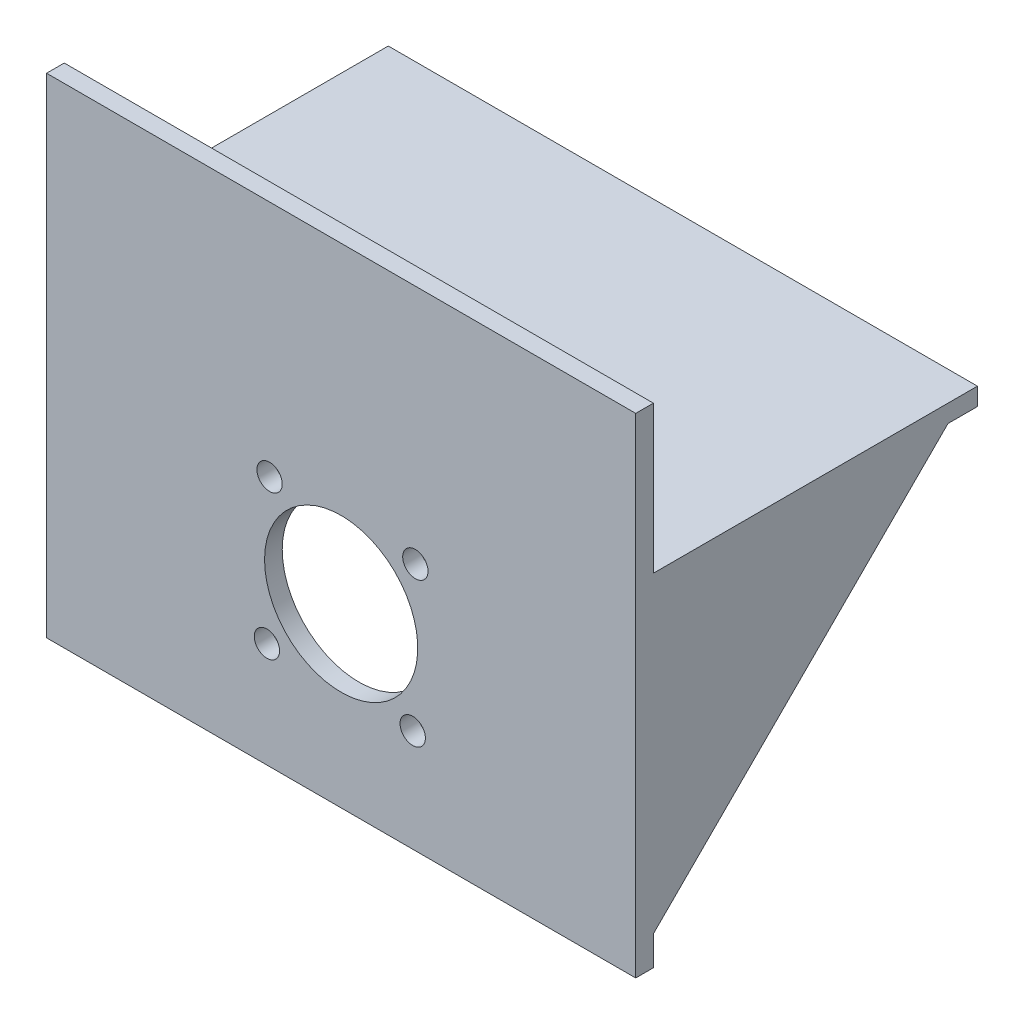
SolidWorks part; units mm, degrees
ref_plane "Front Plane" through (0, 0, 0) normal (0, 0, 1) x (1, 0, 0)
ref_plane "Top Plane" through (0, 0, 0) normal (0, 1, 0) x (1, 0, 0)
ref_plane "Right Plane" through (0, 0, 0) normal (1, 0, 0) x (0, 0, -1)
sketch "Sketch1" plane through (0, 0, 0) normal (0, 1, 0) x (1, 0, 0)
  line L0 (-50, 27.5) -> (50, -27.5) construction
  line L1 (-50, 27.5) -> (50, 27.5)
  line L2 (-50, 27.5) -> (-50, -27.5)
  line L3 (-50, -27.5) -> (50, -27.5)
  line L4 (50, 27.5) -> (50, -27.5)
  dimension "D1" = 55
  dimension "D2" = 100
extrude "Boss-Extrude1" add sketch "Sketch1" along normal blind 3
sketch "Sketch2" plane through (0, 0, 27.5) normal (0, 0, 1) x (1, 0, 0)
  line L0 (-50, 3) -> (50, 3) construction
  line L1 (-50, 28) -> (50, 28)
  line L2 (-50, 28) -> (-50, -55)
  line L3 (-50, -55) -> (50, -55)
  line L4 (50, 28) -> (50, -55)
  line L5 (-50, 3) -> (-50, 0) construction
  line L6 (-50, 0) -> (50, 0) construction
  dimension "D1" = 100
  dimension "25mm" = 25
  dimension "D2" = 55
extrude "Boss-Extrude2" add sketch "Sketch2" along normal blind 3
sketch "Sketch3" plane through (50, 0, 0) normal (1, 0, 0) x (0, 0, -1)
  line L0 (-27.5, 0) -> (22.5, 0)
  line L1 (-27.5, 0) -> (27.5, 0) construction
  line L2 (22.5, 0) -> (-27.5, -50)
  line L3 (-27.5, -55) -> (-27.5, 0) construction
  line L4 (-27.5, -50) -> (-27.5, 0)
  dimension "D1" = 50
  dimension "D2" = 50
extrude "Boss-Extrude3" add sketch "Sketch3" against normal blind 3
sketch "Sketch4" plane through (-50, 0, 0) normal (-1, 0, 0) x (0, 0, 1)
  line L0 (27.5, 0) -> (27.5, -50)
  line L1 (27.5, 0) -> (27.5, -55) construction
  line L2 (27.5, -50) -> (-22.5, 0)
  line L4 (-22.5, 0) -> (27.5, 0)
  dimension "D1" = 50
  dimension "D2" = 50
extrude "Boss-Extrude4" add sketch "Sketch4" against normal blind 3
sketch "Sketch5" plane through (0, 0, 27.5) normal (0, 0, -1) x (-1, 0, 0)
  line L0 (-47, 0) -> (47, -50) construction
  line L1 (-47, 0) -> (47, 0) construction
  line L2 (-47, 0) -> (-47, -50) construction
  line L3 (-47, -50) -> (47, -50) construction
  line L4 (47, 0) -> (47, -50) construction
  circle A0 centre (0, -25) radius 13
  circle A1 centre (0, -25) radius 17.5 construction
  circle A2 centre (12.1488, -12.4041) radius 2.15
  circle A3 centre (12.5959, -37.1488) radius 2.15
  circle A4 centre (-12.1488, -37.5959) radius 2.15
  circle A5 centre (-12.5959, -12.8512) radius 2.15
  point P20 (0, -25)
  dimension "D1" = 26
  dimension "D2" = 35
  dimension "D3" = 4.3
  dimension "D5" = 25
  dimension "D4" = 4
extrude "Cut-Extrude1" cut sketch "Sketch5" against normal through all
